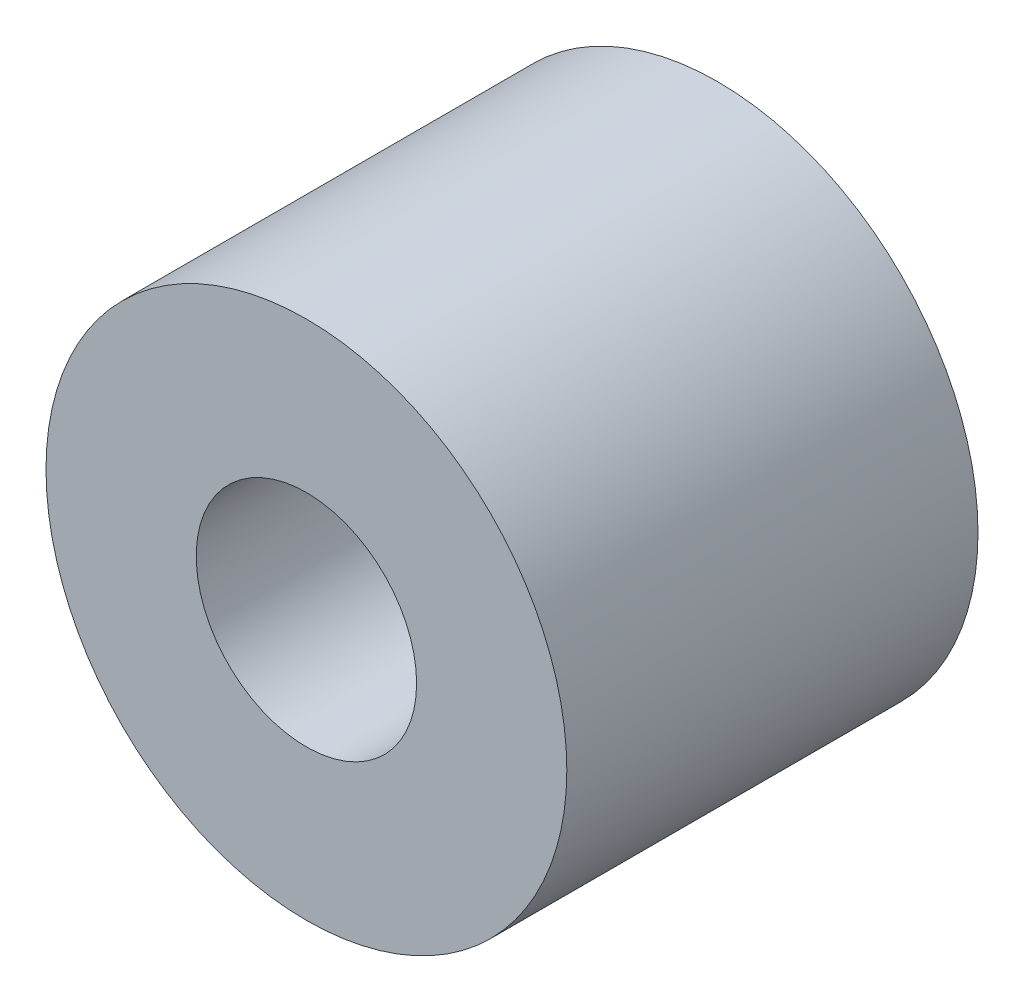
SolidWorks part; units mm, degrees
ref_plane "Front Plane" through (0, 0, 0) normal (0, 0, 1) x (1, 0, 0)
ref_plane "Top Plane" through (0, 0, 0) normal (0, 1, 0) x (1, 0, 0)
ref_plane "Right Plane" through (0, 0, 0) normal (1, 0, 0) x (0, 0, -1)
sketch "Sketch1" plane through (0, 0, 0) normal (0, 0, 1) x (1, 0, 0)
  circle A0 centre (0, 0) radius 6.0325
  dimension "D1" = 12.065
extrude "Boss-Extrude1" add sketch "Sketch1" along normal mid plane 9.525
sketch "Sketch2" plane through (0, 0, 4.7625) normal (0, 0, 1) x (1, 0, 0)
  point P0 (0, 0)
hole_wizard "Tap Drill for 1/4-20 Tap1" positions "Sketch2" profile "Sketch3" hole size "1/4-20" standard "ANSI Inch" end condition through all
sketch "Sketch3" plane through (0, 0, 4.7625) normal (1, 0, 0) x (0, -1, 0)
  line L0 (0, 0) -> (0, 9.525)
  line L1 (0, 9.525) -> (2.5527, 9.525)
  line L2 (2.5527, 9.525) -> (2.5527, 0)
  line L5 (2.5527, 0) -> (0, 0)
  line L11 (0, -6.35) -> (0, 107.95) construction
  dimension "Thru Hole Dia." = 5.1054
  dimension "Thru Hole Depth" = 9.525
cosmetic thread "Cosmetic Thread1" parameters "D2"=6.1054
equation "\"AIRFRAME_OD\"= 3.091in"
equation "\"AIRFRAME_ID\"= 3.00in"
equation "\"FLAT_T\"= 0.125in"
equation "\"NOSE_EXP_L\"= 3.5in"
equation "\"NOSE_SHOULDER_L\"= 5in"
equation "\"MAIN_L\"= 30in"
equation "\"RECO_COUP_L\"= 6in"
equation "\"RECO_SWITCH_L\"= 1.5in"
equation "\"DROGUE_L\"= 14in"
equation "\"ATS_FORE_COUP_L\"= 4in"
equation "\"ATS_AFT_COUP_L\"= 2.5in"
equation "\"LOWER_L\"= 16in"
equation "\"FIN_N\"= 4"
equation "\"CR_AFT_X\"= 0.5in"
equation "\"CR_FORE_X\"= 6in"
